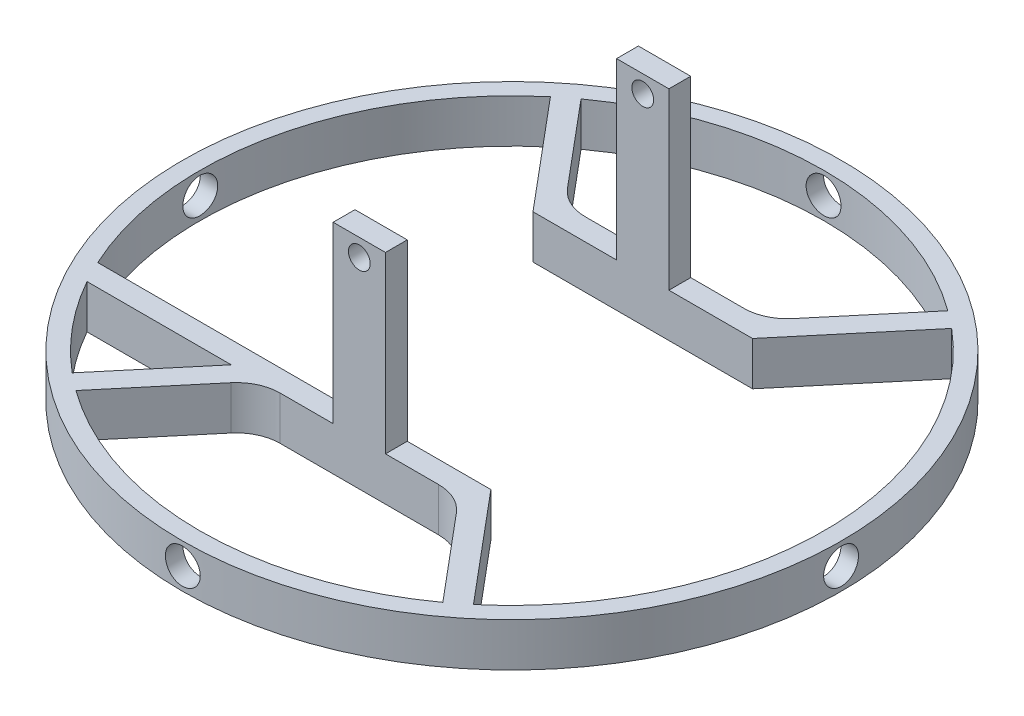
SolidWorks part; units mm, degrees
ref_plane "Alzado" through (0, 0, 0) normal (0, 0, 1) x (1, 0, 0)
ref_plane "Planta" through (0, 0, 0) normal (0, 1, 0) x (1, 0, 0)
ref_plane "Vista lateral" through (0, 0, 0) normal (1, 0, 0) x (0, 0, -1)
sketch "Croquis1" plane through (0, 0, 0) normal (0, 1, 0) x (1, 0, 0)
  line L1 (-15, -15) -> (15, -15)
  line L2 (-15, -15) -> (-15, 15)
  line L3 (-15, 15) -> (15, 15)
  line L4 (15, -15) -> (15, 15)
  line L5 (-15, -15) -> (15, 15) construction
  line L6 (-15, 15) -> (15, -15) construction
  circle A0 centre (0, 0) radius 11
  point P0 (0, 0)
  dimension "D3" = 22
  dimension "D4" = 4
  dimension "D1" = 30
  dimension "D2" = 30
sketch "Croquis2" plane through (0, 0, 0) normal (0, 1, 0) x (1, 0, 0)
  line L0 (-15, -15) -> (15, 15) construction
  line L2 (0, 15) -> (0, 0) construction
  line L4 (0, 0) -> (-35.79, 0) construction
  line L19 (12.5865, 15) -> (-12.5865, 15)
  line L20 (-12.5865, 15) -> (-23.0054, 27.4167)
  line L21 (12.5865, 15) -> (23.0054, 27.4167)
  line L22 (11.4207, 17.5) -> (21.0903, 29.0237)
  line L23 (11.4207, 17.5) -> (-11.4207, 17.5)
  line L24 (-11.4207, 17.5) -> (-21.0903, 29.0237)
  line L25 (12.5865, -15) -> (23.0054, -27.4167)
  line L26 (11.4207, -17.5) -> (21.0903, -29.0237)
  line L27 (11.4207, -17.5) -> (-11.4207, -17.5)
  line L28 (-11.4207, -17.5) -> (-21.0903, -29.0237)
  line L29 (-12.5865, -15) -> (-23.0054, -27.4167)
  line L30 (12.5865, -15) -> (-12.5865, -15)
  circle A0 centre (0, 0) radius 37.79
  circle A2 centre (0, 0) radius 35.79
  point P9 (0, 15)
  point P34 (0, 0)
  dimension "D1" = 75.58
  dimension "D3" = 15
  dimension "D4" = 2.5
  dimension "D5" = 130
  dimension "D6" = 130
  dimension "D2" = 2
extrude "Saliente-Extruir1" add sketch "Croquis2" along normal blind 5
ref_plane "Plano1" through (0, 0, 15) normal (0, 0, 1) x (1, 0, 0)
sketch "Croquis3" plane through (0, 0, 0) normal (0, 1, 0) x (1, 0, 0)
  line L1 (-15, -15) -> (15, -15)
  line L2 (-15, -15) -> (-15, 15)
  line L3 (-15, 15) -> (15, 15)
  line L4 (15, -15) -> (15, 15)
  line L5 (-15, -15) -> (15, 15) construction
  line L6 (-15, 15) -> (15, -15) construction
  line L7 (-12.5, -12.5) -> (-12.5, 12.5)
  line L8 (-12.5, 12.5) -> (12.5, 12.5)
  line L9 (12.5, -12.5) -> (12.5, 12.5)
  line L10 (-12.5, -12.5) -> (12.5, -12.5)
  dimension "D1" = 2.5
  dimension "D2" = 30
sketch "Croquis4" plane through (0, 0, 15) normal (0, 0, 1) x (1, 0, 0)
  line L0 (-15, 0) -> (15, 0) construction
  line L1 (-3, 25) -> (3, 25)
  line L2 (-3, 25) -> (-3, 0)
  line L3 (-3, 0) -> (3, 0)
  line L4 (3, 25) -> (3, 0)
  line L5 (-3, 25) -> (3, 0) construction
  line L6 (-3, 0) -> (3, 25) construction
  point P0 (0, 12.5)
  dimension "D1" = 25
  dimension "D2" = 6
  dimension "D3" = 3
extrude "Saliente-Extruir3" add sketch "Croquis4" along normal blind 2.5
mirror "Simetría1" about plane through (0, 0, 0) normal (0, 0, 1) of "Saliente-Extruir3"
sketch "Croquis5" plane through (0, 0, -17.5) normal (0, 0, -1) x (-1, 0, 0)
  line L0 (0, 25) -> (0, 23) construction
  line L1 (-3, 25) -> (3, 25) construction
  line L2 (0, 23) -> (3, 23) construction
  line L3 (3, 25) -> (3, 5) construction
  circle A0 centre (0, 23) radius 1.25
  dimension "D1" = 2
  dimension "D2" = 2.5
extrude "Cortar-Extruir1" cut sketch "Croquis5" against normal through all both and the other way through all
fillet "Redondeo1" radius 5 4 edges at (11.4207, 2.5, -17.5) (-11.4207, 2.5, -17.5) (11.4207, 2.5, 17.5) (-11.4207, 2.5, 17.5)
sketch "Croquis6" plane through (0, 0, 0) normal (0, 0, 1) x (1, 0, 0)
  line L0 (0, 0) -> (0, 5) construction
  line L2 (37.79, 5) -> (-37.79, 5) construction
  circle A0 centre (0, 2.5) radius 2
  dimension "D1" = 4
extrude "Cortar-Extruir2" cut sketch "Croquis6" against normal blind 17 from offset 50
pattern_circular "MatrizC1" count 4 over 360 of "Cortar-Extruir2"
sketch "Croquis8" plane through (0, 5, 0) normal (0, 1, 0) x (1, 0, 0)
  line L0 (-12.5865, -15) -> (-32.495, -15)
  line L1 (-14.6842, -17.5) -> (-31.2198, -17.5)
  line L2 (-3, -17.5) -> (-3, -15) construction
  line L3 (-3, -17.5) -> (-3, -15)
  line L4 (-12.5865, -15) -> (-23.0054, -27.4167) construction
  line L5 (-12.5865, -15) -> (-14.6842, -17.5)
  line L6 (-12.5865, -17.5) -> (-32.495, -17.5) construction
  arc A0 (-23.0054, 27.4167) -> (-23.0054, -27.4167) centre (0, 0) ccw construction
  arc A1 (-32.495, -15) -> (-31.2198, -17.5) centre (0, 0) ccw
  line M20 (-12.5865, -15) -> (-23.0054, -27.4167)
  arc M21 (-23.0054, -27.4167) -> (-23.0054, 27.4167) centre (0, 0) cw
  dimension "D1" = 2.5
extrude "Saliente-Extruir5" add sketch "Croquis8" against normal blind 5 contours L1 L0 M20 M21
